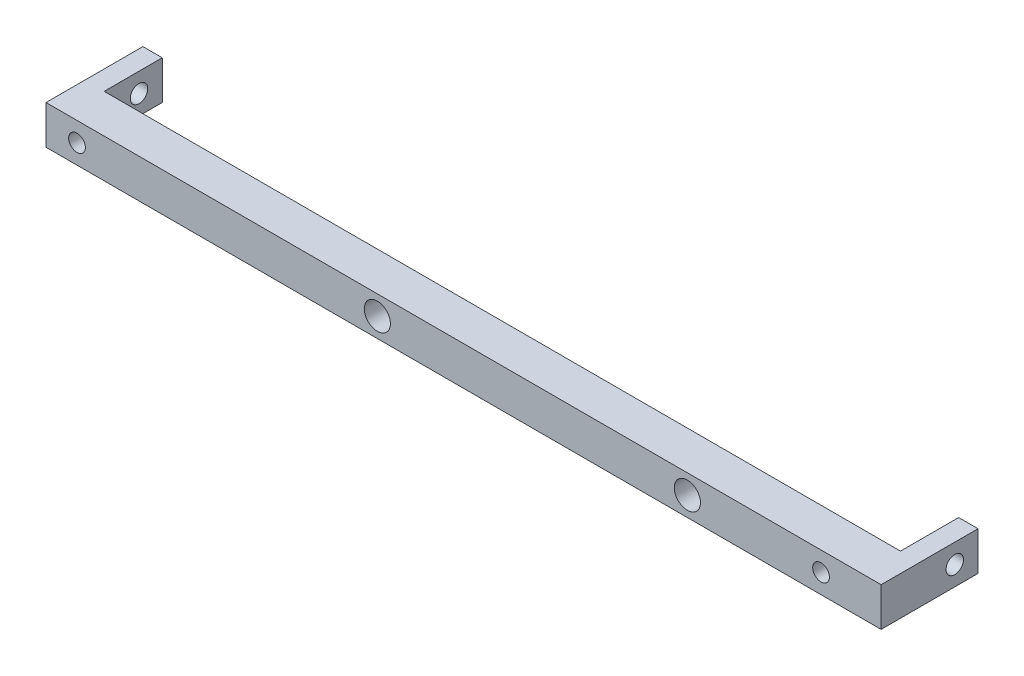
SolidWorks part; units mm, degrees
material "6061-T6 Al"
ref_plane "Front" through (0, 0, 0) normal (0, 0, 1) x (1, 0, 0)
ref_plane "Top" through (0, 0, 0) normal (0, 1, 0) x (1, 0, 0)
ref_plane "Right" through (0, 0, 0) normal (1, 0, 0) x (0, 0, -1)
ref_plane "Plane1" through (0, 5, 0) normal (0, 1, 0) x (1, 0, 0)
sketch "Sketch1" plane through (0, 5, 0) normal (0, 1, 0) x (1, 0, 0)
  line L0 (107.75, -2) -> (107.75, 23)
  line L1 (107.75, 23) -> (-107.75, 23)
  line L2 (-107.75, 23) -> (-107.75, -2)
  line L3 (-107.75, -2) -> (107.75, -2)
extrude "Boss-Extrude1" add sketch "Sketch1" against normal blind 10
sketch "Sketch2" plane through (0, -5, 0) normal (0, -1, 0) x (1, 0, 0)
  line L0 (-102.75, -23) -> (102.75, -23)
  line L1 (102.75, -23) -> (102.75, -8)
  line L2 (102.75, -8) -> (-102.75, -8)
  line L3 (-102.75, -8) -> (-102.75, -23)
extrude "Cut-Extrude1" cut sketch "Sketch2" against normal through all
sketch "Sketch3" plane through (0, 0, -8) normal (0, 0, -1) x (-1, 0, 0)
  line L0 (17.25, 3.5) -> (-52.75, 3.5)
  line L1 (-52.75, 3.5) -> (-52.75, -3.5)
  line L2 (-52.75, -3.5) -> (17.25, -3.5)
  line L3 (17.25, -3.5) -> (17.25, 3.5)
extrude "Cut-Extrude2" cut sketch "Sketch3" against normal blind 8.5
sketch "Sketch4" plane through (0, 0, -8) normal (0, 0, -1) x (-1, 0, 0)
  line L0 (82, 3.5) -> (27.25, 3.5)
  line L1 (27.25, 3.5) -> (27.25, -3.5)
  line L2 (27.25, -3.5) -> (82, -3.5)
  line L3 (82, -3.5) -> (82, 3.5)
extrude "Cut-Extrude3" cut sketch "Sketch4" against normal blind 8.5
sketch "Sketch5" plane through (0, 0, -8) normal (0, 0, -1) x (-1, 0, 0)
  line L0 (-62.75, -3.5) -> (-62.75, 3.5)
  line L1 (-62.75, 3.5) -> (-82, 3.5)
  line L2 (-82, 3.5) -> (-82, -3.5)
  line L3 (-82, -3.5) -> (-62.75, -3.5)
extrude "Cut-Extrude4" cut sketch "Sketch5" against normal blind 8.5
hole_wizard "Ø4.5 (4.5) Diameter Hole1" positions "Sketch7" profile "Sketch6" hole size "Ø4.5" standard "ANSI Metric"
sketch "Sketch7" plane through (-102.75, 0, 0) normal (1, 0, 0) x (0, 0, -1)
  point P0 (17, 0)
sketch "Sketch6" plane through (-102.75, 0, -17) normal (0, 1, 0) x (0, 0, -1)
  line L0 (0, 0) -> (0, 5)
  line L1 (0, 5) -> (2.25, 5)
  line L2 (2.25, 5) -> (2.25, 0)
  line L5 (2.25, 0) -> (0, 0)
  line L11 (0, -6.35) -> (0, 107.95) construction
  dimension "Thru Hole Dia." = 4.5
  dimension "Thru Hole Depth" = 5
hole_wizard "M4 Clearance Hole1" positions "Sketch9" profile "Sketch8" hole size "M4" standard "ANSI Metric" end condition through all
sketch "Sketch9" plane through (0, 0, 2) normal (0, 0, 1) x (1, 0, 0)
  line L0 (-107.75, 0) -> (-99.7515, 0) construction
  line L1 (-107.75, -5) -> (-107.75, 5) construction
  line L2 (-99.7515, 0) -> (92.2496, 0) construction
  point P0 (-99.7515, 0)
  point P1 (92.2496, 0)
  dimension "D1" = 7.9985
  dimension "D2" = 199.9996
sketch "Sketch8" plane through (-99.7515, 0, 2) normal (1, 0, 0) x (0, -1, 0)
  line L0 (0, 0) -> (0, 25)
  line L1 (0, 25) -> (2.155, 25)
  line L2 (2.155, 25) -> (2.155, 0)
  line L5 (2.155, 0) -> (0, 0)
  line L11 (0, -6.35) -> (0, 107.95) construction
  dimension "Thru Hole Dia." = 4.31
  dimension "Thru Hole Depth" = 25
hole_wizard "Tapped Hole for 1/4-20 Helicoil1" positions "Sketch11" profile "Sketch10" tap size "1/4-20" standard "Helicoil® Inch"
sketch "Sketch11" plane through (0, 0, 2) normal (0, 0, 1) x (1, 0, 0)
  point P0 (57.75, 0)
  point P1 (-22.25, 0)
sketch "Sketch10" plane through (57.75, 0, 2) normal (1, 0, 0) x (0, -1, 0)
  line L0 (0, 0) -> (0, 22.5528)
  line L1 (0, 22.5528) -> (3.3782, 20.523)
  line L2 (3.3782, 20.523) -> (3.3782, 0)
  line L5 (3.3782, 0) -> (0, 0)
  line L10 (0, 22.5528) -> (-3.3782, 20.523) construction
  line L11 (0, -6.35) -> (0, 107.95) construction
  dimension "Tap Drill Dia." = 6.7564
  dimension "Tap Drill Depth" = 20.523
  dimension "Drill Angle" = 118
hole_wizard "Ø4.5 (4.5) Diameter Hole2" positions "Sketch13" profile "Sketch12" hole size "Ø4.5" standard "ANSI Metric"
sketch "Sketch13" plane through (107.75, 0, 0) normal (1, 0, 0) x (0, 0, -1)
  point P0 (17, 0)
sketch "Sketch12" plane through (107.75, 0, -17) normal (0, 1, 0) x (0, 0, -1)
  line L0 (0, 0) -> (0, 215.5)
  line L1 (0, 215.5) -> (2.25, 215.5)
  line L2 (2.25, 215.5) -> (2.25, 0)
  line L5 (2.25, 0) -> (0, 0)
  line L11 (0, -6.35) -> (0, 107.95) construction
  dimension "Thru Hole Dia." = 4.5
  dimension "Thru Hole Depth" = 215.5
fillet "Fillet1" radius 3 12 edges at (-27.25, 3.5, -3.75) (62.75, 3.5, -3.75) (82, -3.5, -3.75) (52.75, -3.5, -3.75) (-27.25, -3.5, -3.75) (52.75, 3.5, -3.75) (62.75, -3.5, -3.75) (-17.25, 3.5, -3.75) (82, 3.5, -3.75) (-82, 3.5, -3.75) (-17.25, -3.5, -3.75) (-82, -3.5, -3.75)
